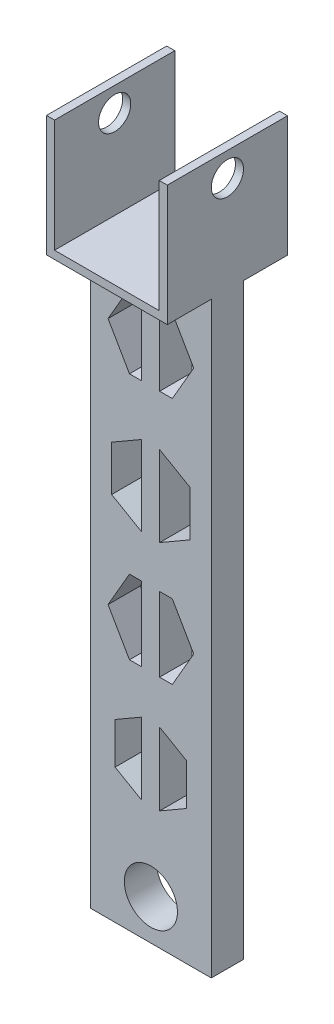
SolidWorks part; units mm, degrees
ref_plane "前视基准面" through (0, 0, 0) normal (0, 0, 1) x (1, 0, 0)
ref_plane "上视基准面" through (0, 0, 0) normal (0, 1, 0) x (1, 0, 0)
ref_plane "右视基准面" through (0, 0, 0) normal (1, 0, 0) x (0, 0, -1)
sketch "草图1" plane through (0, 0, 0) normal (0, 1, 0) x (1, 0, 0)
  line L1 (-19.8655, -2.2877) -> (-4.8655, -2.2877)
  line L2 (-19.8655, -2.2877) -> (-19.8655, -6.2877)
  line L3 (-19.8655, -6.2877) -> (-4.8655, -6.2877)
  line L4 (-4.8655, -2.2877) -> (-4.8655, -6.2877)
extrude "凸台-拉伸1" add sketch "草图1" along normal blind 85
sketch "草图11" plane through (0, 0, 2.2877) normal (0, 0, -1) x (-1, 0, 0)
  line L0 (12.3655, 0) -> (12.3655, 5)
  line L1 (4.8655, 0) -> (19.8655, 0) construction
sketch "草图17" plane through (0, 0, 2.2877) normal (0, 0, -1) x (-1, 0, 0)
  line L0 (19.8655, 85) -> (19.8655, 73)
  line L1 (4.8655, 88) -> (19.8655, 88)
  line L2 (4.8655, 88) -> (4.8655, 73)
  line L3 (4.8655, 73) -> (19.8655, 73)
  line L4 (19.8655, 88) -> (19.8655, 73)
  line L5 (19.8655, 85) -> (19.8655, 0) construction
  line M4 (19.8655, 0) -> (19.8655, 85)
  line M5 (19.8655, 85) -> (4.8655, 85)
  line M6 (4.8655, 85) -> (4.8655, 0)
extrude "凸台-拉伸2" add sketch "草图17" along normal blind 10 and the other way blind 14 contours L3 M6 M4 M5 | L4 L1 L2 M5
sketch "草图18" plane through (0, 88, 0) normal (0, 1, 0) x (1, 0, 0)
  line L1 (-5.8655, -16.2877) -> (-18.8655, -16.2877)
  line L2 (-5.8655, -16.2877) -> (-5.8655, 7.7123)
  line L3 (-5.8655, 7.7123) -> (-18.8655, 7.7123)
  line L4 (-18.8655, -16.2877) -> (-18.8655, 7.7123)
  line L5 (-5.8655, -16.2877) -> (-18.8655, 7.7123) construction
  line L6 (-5.8655, 7.7123) -> (-18.8655, -16.2877) construction
  point P0 (-12.3655, -4.2877)
  point P7 (0, 0)
  point P8 (0, 0)
extrude "切除-拉伸4" cut sketch "草图18" against normal blind 14
sketch "草图20" plane through (-19.8655, 0, 0) normal (-1, 0, 0) x (0, 0, 1)
  line L1 (-3.1756, 73) -> (11.751, 73)
  line L2 (-3.1756, 73) -> (-3.1756, 88)
  line L3 (-3.1756, 88) -> (11.751, 88)
  line L4 (11.751, 73) -> (11.751, 88)
  line L5 (-3.1756, 73) -> (11.751, 88) construction
  line L6 (-3.1756, 88) -> (11.751, 73) construction
  line L7 (-3.1756, 88) -> (-7.7123, 88)
  line L8 (-7.7123, 88) -> (-7.7123, 73)
  line L9 (-7.7123, 73) -> (-3.1756, 73)
  line L10 (11.751, 73) -> (16.2877, 73)
  line L11 (16.2877, 73) -> (16.2877, 88)
  line L13 (16.2877, 88) -> (11.751, 88)
  point P0 (4.2877, 80.5)
extrude "切除-拉伸6" cut sketch "草图20" against normal blind 18
sketch "草图21" plane through (-19.8655, 0, 0) normal (-1, 0, 0) x (0, 0, 1)
  line L0 (6.2877, 1.1694) -> (6.2877, 8.8609)
  line L1 (6.2877, 73) -> (6.2877, 0) construction
  line L2 (6.2877, 8.8609) -> (6.2877, 5.0151)
  line L3 (6.2877, 5.0151) -> (4.2877, 5.0151)
  line L4 (4.2877, 5.0151) -> (4.2877, 85.0151)
  circle A0 centre (4.2877, 85.0151) radius 2
extrude "切除-拉伸7" cut sketch "草图21" against normal blind 39
sketch "草图22" plane through (0, 0, 2.2877) normal (0, 0, -1) x (-1, 0, 0)
  circle A0 centre (12.3655, 5) radius 3.3
extrude "切除-拉伸8" cut sketch "草图22" against normal blind 4
sketch "草图23" plane through (0, 0, 6.2877) normal (0, 0, 1) x (1, 0, 0)
  line L1 (-7.0439, 64.5049) -> (-9.7047, 69.1134)
  line L2 (-9.7047, 69.1134) -> (-15.0262, 69.1134)
  line L3 (-15.0262, 69.1134) -> (-17.687, 64.5049)
  line L4 (-17.687, 64.5049) -> (-15.0262, 59.8963)
  line L5 (-15.0262, 59.8963) -> (-9.7047, 59.8963)
  line L6 (-9.7047, 59.8963) -> (-7.0439, 64.5049)
  line L7 (-12.3655, 54.2539) -> (-17.2409, 51.4391)
  line L8 (-17.2409, 51.4391) -> (-17.2409, 45.8094)
  line L9 (-17.2409, 45.8094) -> (-12.3655, 42.9946)
  line L10 (-12.3655, 42.9946) -> (-7.4901, 45.8094)
  line L11 (-7.4901, 45.8094) -> (-7.4901, 51.4391)
  line L12 (-7.4901, 51.4391) -> (-12.3655, 54.2539)
  line L13 (-7.0439, 33.7519) -> (-9.7047, 38.3605)
  line L14 (-9.7047, 38.3605) -> (-15.0262, 38.3605)
  line L15 (-15.0262, 38.3605) -> (-17.687, 33.7519)
  line L16 (-17.687, 33.7519) -> (-15.0262, 29.1433)
  line L17 (-15.0262, 29.1433) -> (-9.7047, 29.1433)
  line L18 (-9.7047, 29.1433) -> (-7.0439, 33.7519)
  line L19 (-12.3655, 24.398) -> (-16.8084, 21.8329)
  line L20 (-16.8084, 21.8329) -> (-16.8084, 16.7026)
  line L21 (-16.8084, 16.7026) -> (-12.3655, 14.1374)
  line L22 (-12.3655, 14.1374) -> (-7.9225, 16.7026)
  line L23 (-7.9225, 16.7026) -> (-7.9225, 21.8329)
  line L24 (-7.9225, 21.8329) -> (-12.3655, 24.398)
  line L25 (-13.5379, 69.1134) -> (-11.2832, 69.1134)
  line L26 (-13.5379, 69.1134) -> (-13.5379, 14.1374)
  line L27 (-13.5379, 14.1374) -> (-11.2832, 14.1374)
  line L28 (-11.2832, 69.1134) -> (-11.2832, 14.1374)
  circle A0 centre (-12.3655, 64.5049) radius 4.6086 construction
  circle A1 centre (-12.3655, 48.6242) radius 4.8754 construction
  circle A2 centre (-12.3655, 33.7519) radius 4.6086 construction
  circle A3 centre (-12.3655, 19.2677) radius 4.443 construction
extrude "切除-拉伸9" cut sketch "草图23" against normal blind 4 contours L26 L2 L3 L4 L5 | L2 L28 L5 L6 L1 | L26 L7 L8 L9 | L12 L28 L10 L11 | L26 L14 L15 L16 L17 | L14 L28 L17 L18 L13 | L26 L19 L20 L21 | L24 L28 L22 L23
